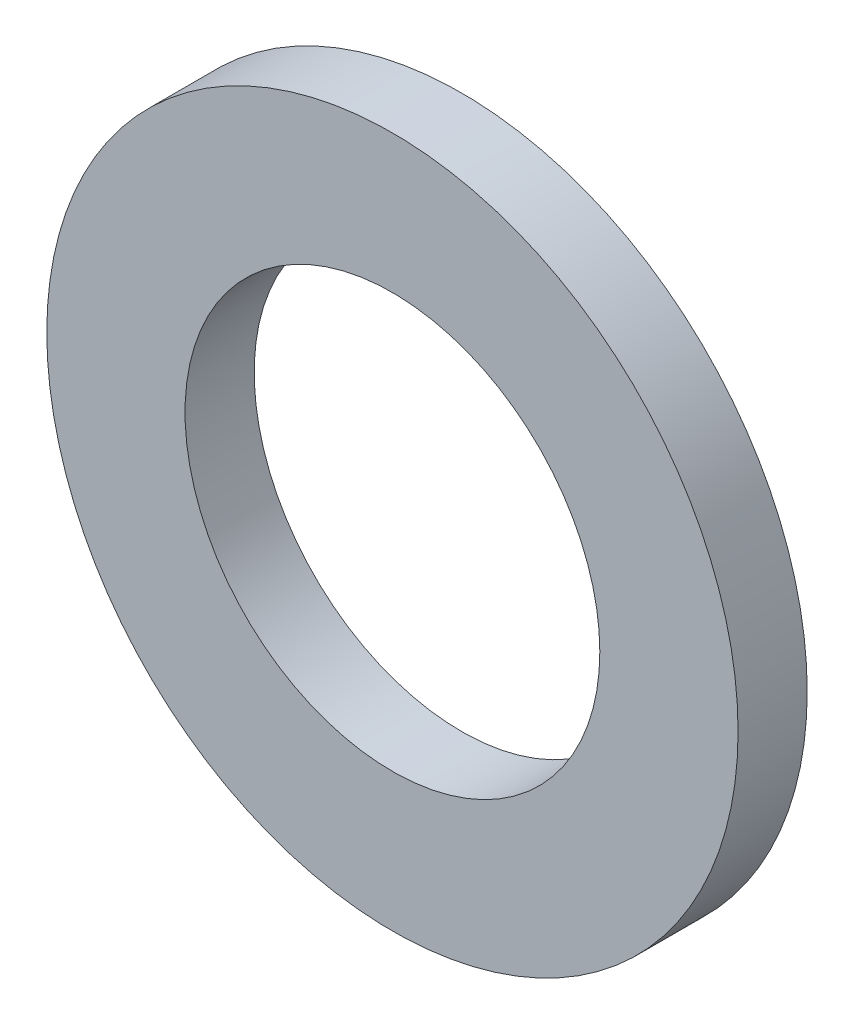
SolidWorks part; units mm, degrees
ref_plane "前视基准面" through (0, 0, 0) normal (0, 0, 1) x (1, 0, 0)
ref_plane "上视基准面" through (0, 0, 0) normal (0, 1, 0) x (1, 0, 0)
ref_plane "右视基准面" through (0, 0, 0) normal (1, 0, 0) x (0, 0, -1)
sketch "草图1" plane through (0, 0, 0) normal (0, 0, 1) x (1, 0, 0)
  circle A0 centre (0, 0) radius 1.5
  circle A1 centre (0, 0) radius 2.5
  dimension "D1" = 3
  dimension "D2" = 5
extrude "凸台-拉伸1" add sketch "草图1" along normal blind 0.5
